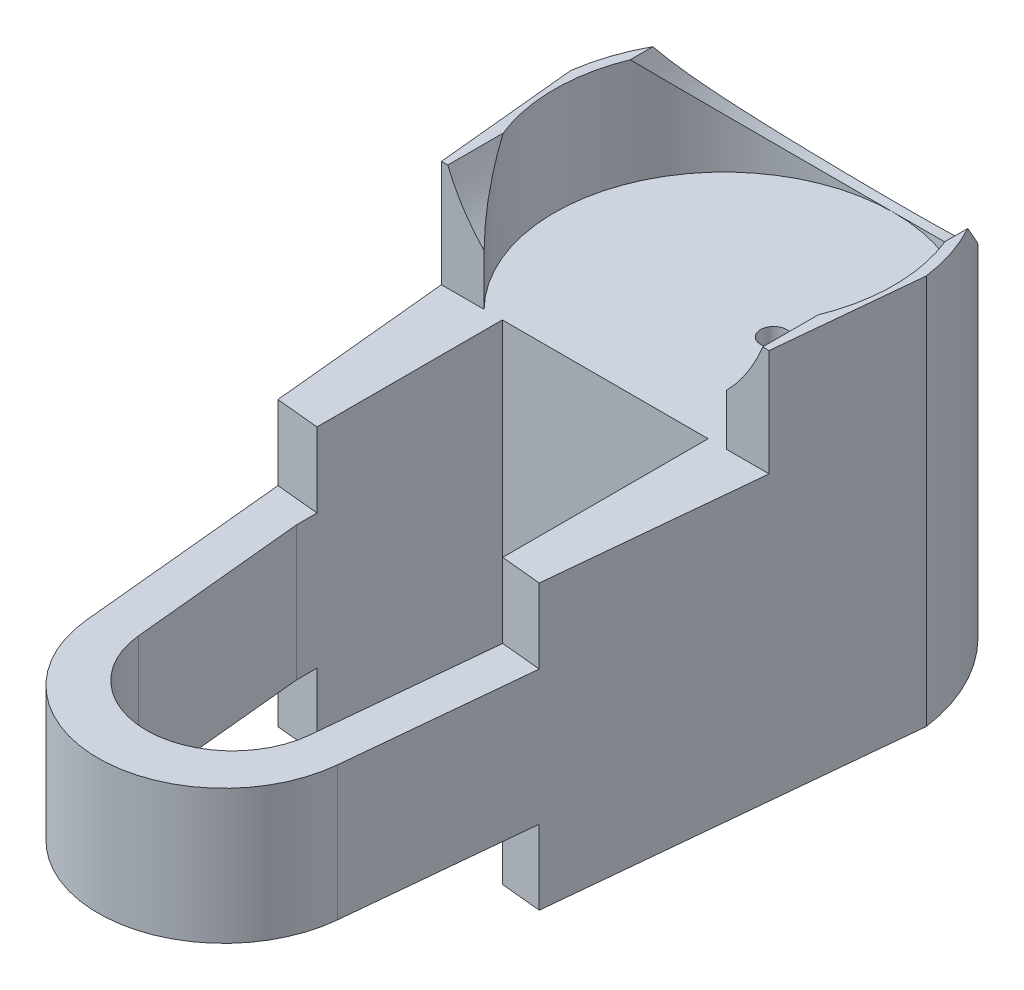
SolidWorks part; units mm, degrees
ref_plane "Front Plane" through (0, 0, 0) normal (0, 0, 1) x (1, 0, 0)
ref_plane "Top Plane" through (0, 0, 0) normal (0, 1, 0) x (1, 0, 0)
ref_plane "Right Plane" through (0, 0, 0) normal (1, 0, 0) x (0, 0, -1)
sketch "Sketch1" plane through (0, 0, 0) normal (0, 1, 0) x (1, 0, 0)
  line L0 (-21.209, -21.2151) -> (21.209, -21.2151)
  line L1 (-21.209, -21.209) -> (21.209, -21.209)
  line L2 (-21.209, -21.209) -> (-21.209, 21.209)
  line L3 (-21.209, 21.209) -> (21.209, 21.209)
  line L4 (21.209, -21.209) -> (21.209, 21.209)
  line L5 (-21.209, -21.209) -> (21.209, 21.209) construction
  line L6 (-21.209, 21.209) -> (21.209, -21.209) construction
  line L7 (-21.209, -21.2151) -> (-21.209, 21.2029)
  line L8 (-21.209, 21.2029) -> (21.209, 21.2029)
  line L9 (21.209, -21.2151) -> (21.209, 21.2029)
  line L10 (-21.209, -21.2151) -> (-4.8245, -4.8306) construction
  line L11 (-21.209, -66.9351) -> (21.209, -66.9351)
  line L12 (-36.6585, 5.0151) -> (-25.8562, -105.5982)
  line L13 (0, -55) -> (0, 55) construction
  line L14 (36.6585, 5.0151) -> (25.8562, -105.5982)
  line L15 (0.4439, 0.4378) -> (21.209, 21.2029) construction
  line L16 (-21.209, -66.929) -> (21.209, -66.929)
  line L17 (0.2749, -0.2809) -> (4.4443, -4.4503) construction
  line L18 (-21.209, -66.929) -> (-21.209, -24.511)
  line L19 (-21.209, -24.511) -> (21.209, -24.511)
  line L20 (21.209, -66.929) -> (21.209, -24.511)
  line L21 (-21.209, -66.9351) -> (-21.209, -24.5171)
  line L22 (-21.209, -24.5171) -> (21.209, -24.5171)
  line L23 (21.209, -66.9351) -> (21.209, -24.5171)
  line L24 (-21.209, -66.929) -> (21.209, -24.511) construction
  line L25 (-21.209, -24.511) -> (21.209, -66.929) construction
  line L26 (-21.209, -66.9351) -> (-4.8245, -50.5506) construction
  line L27 (0.4439, -45.2822) -> (21.209, -24.5171) construction
  arc A1 (-25.8562, -105.5982) -> (25.8562, -105.5982) centre (0, -103.0732) ccw
  arc A3 (36.6585, 5.0151) -> (-36.6585, 5.0151) centre (0, 0) ccw
  point P0 (0, 0)
  point P8 (0, -0.0061)
  point P17 (0, -45.72)
  point P30 (0, -45.7261)
  dimension "D5" = 37
  dimension "D1" = 42.418
  dimension "D2" = 42.418
  dimension "D3" = 2
  dimension "D4" = 2
extrude "Boss-Extrude1" add sketch "Sketch1" along normal blind 58.42 contours L14 A3 L12 A1 L4 L1 L2 L3 L9 L0 L7 L8 | L8 L2 L1 L4
sketch "Sketch2" plane through (0, 58.42, 0) normal (0, 1, 0) x (1, 0, 0)
  line L0 (-21.209, -66.9351) -> (-17.6812, -103.0584)
  line L3 (21.209, -66.9351) -> (17.6812, -103.0584)
  line L4 (-36.6585, 5.0151) -> (-25.8562, -105.5982) construction
  line L5 (36.6585, 5.0151) -> (25.8562, -105.5982) construction
  line L7 (-21.209, -66.9351) -> (21.209, -66.9351) construction
  line L8 (-21.209, -66.9351) -> (21.209, -66.9351)
  arc A0 (-17.6812, -103.0584) -> (17.6812, -103.0584) centre (0, -101.3316) ccw
  dimension "D1" = 180
  dimension "D2" = 180
sketch "Sketch3" plane through (35.8271, 0, 3.4988) normal (0.9953, 0, 0.0972) x (0.0972, 0, -0.9953)
  line L0 (-102.5851, 58.42) -> (-102.5851, 0) construction
  line L1 (-140.6851, 15.367) -> (-64.4851, 15.367)
  line L3 (-140.6851, 43.053) -> (-64.4851, 43.053)
  line L5 (-140.6851, 15.367) -> (-102.5851, 29.21) construction
  line L6 (-102.5851, 29.21) -> (-64.4851, 15.367) construction
  line L7 (-64.4851, 43.053) -> (-64.4851, 58.42)
  line L8 (8.5544, 58.42) -> (-102.5851, 58.42) construction
  line L9 (-64.4851, 58.42) -> (-140.6851, 58.42)
  line L10 (-140.6851, 58.42) -> (-140.6851, 43.053)
  line L11 (-140.6851, 0) -> (-64.4851, 0)
  line L12 (8.5544, 0) -> (-102.5851, 0) construction
  line L13 (-64.4851, 0) -> (-64.4851, 15.367)
  line L14 (-140.6851, 15.367) -> (-140.6851, 0)
  point P0 (-102.5851, 29.21)
  line M3 (-102.5851, 0) -> (8.5544, 0)
  line M6 (-102.5851, 58.42) -> (-102.5851, 0)
  dimension "D1" = 27.686
  dimension "D2" = 76.2
extrude "Cut-Extrude3" cut sketch "Sketch2" against normal blind 68.58 contours L0 A0 L3 L8
extrude "Cut-Extrude4" cut sketch "Sketch3" against normal through all contours L1 L14 L11 M6 | L13 L1 M3 M6 | L9 L10 L3 L7
ref_plane "Plane2" through (0, 0, 21.209) normal (0, 0, 1) x (1, 0, 0)
sketch "Sketch7" plane through (0, 0, 21.209) normal (0, 0, 1) x (1, 0, 0)
  line L0 (0, 58.42) -> (0, 93.35) construction
  line L1 (-21.209, 58.42) -> (21.209, 58.42) construction
  line L2 (-34.93, 59.9091) -> (-34.93, 93.35)
  line L3 (34.93, 59.9091) -> (34.93, 93.35)
  line L4 (-34.93, 59.9091) -> (34.93, 59.9091)
  line L5 (-34.93, 93.35) -> (34.93, 93.35)
  line L6 (-34.93, 59.9091) -> (-34.93, 55.4014)
  line L7 (-34.93, 55.4014) -> (34.93, 55.4014)
  line L8 (34.93, 55.4014) -> (34.93, 59.9091)
  line L9 (-34.93, 55.4014) -> (-40.0147, 55.4014)
  line L10 (-40.0147, 55.4014) -> (-40.0147, 94.2075)
  line L11 (-34.93, 93.35) -> (-40.0147, 94.2075)
  line L12 (34.93, 55.4014) -> (41.4804, 55.4014)
  line L13 (41.4804, 55.4014) -> (41.4804, 93.35)
  line L14 (41.4804, 93.35) -> (34.93, 93.35)
  arc A0 (-34.93, 93.35) -> (34.93, 93.35) centre (0, 93.35) ccw
  dimension "D1" = 34.93
extrude "Boss-Extrude6" add sketch "Sketch7" against normal blind 60 and the other way up to surface (3.302 mm away) contours A0 L2 L4 | L7 L8 L4 L6 | A0 L4 L3 | L2 L11 L10 L9 L6 | L13 L14 L3 L8 L12
sketch "Sketch9" plane through (0, 0, 0) normal (0, -1, 0) x (1, 0, 0)
  line L0 (36.6585, -5.0151) -> (29.5593, 67.6786) construction
  line L1 (-36.6585, -5.0151) -> (-30.1286, 61.8496) construction
  line L2 (36.6585, -5.0151) -> (29.5593, 67.6786)
  line L3 (-36.6585, -5.0151) -> (-30.1286, 61.8496)
  line L4 (29.5593, 67.6786) -> (73.6606, -15.3241)
  line L5 (73.6606, -15.3241) -> (14.2721, -84.2116)
  line L6 (14.2721, -84.2116) -> (-60.0286, -39.8694)
  line L7 (-60.0286, -39.8694) -> (-30.1286, 61.8496)
  arc A0 (-36.6585, -5.0151) -> (36.6585, -5.0151) centre (0, 0) ccw construction
  arc A1 (-36.6585, -5.0151) -> (36.6585, -5.0151) centre (0, 0) ccw
extrude "Cut-Extrude9" cut sketch "Sketch9" against normal blind 106
sketch "Sketch4" plane through (0, 58.42, 0) normal (0, 1, 0) x (1, 0, 0)
  line L0 (9.8, -24.511) -> (9.8, 0.389) construction
  circle A0 centre (9.8, 0.389) radius 2.667
  dimension "D2" = 5.334
  dimension "D1" = 24.9
extrude "Cut-Extrude6" cut sketch "Sketch4" against normal blind 20 and the other way blind 106
sketch "Sketch10" plane through (35.8271, 0, 3.4988) normal (0.9953, 0, 0.0972) x (0.0972, 0, -0.9953)
  line L0 (-21.1121, 80.4421) -> (1.8262, 80.4421)
  line L1 (-21.1121, 58.42) -> (-21.1121, 84.4421) construction
  line L2 (-21.1121, 80.4421) -> (-21.1121, 84.4421)
  line L3 (1.8262, 80.4421) -> (48.3524, 80.4421)
  line L4 (48.3524, 80.4421) -> (47.2155, 104.0447)
  line L5 (47.2155, 104.0447) -> (-21.1121, 100.7536)
  line L6 (-21.1121, 100.7536) -> (-21.1121, 84.4421)
  line L7 (-21.1121, 80.4421) -> (-34.4127, 80.4421)
  line L8 (-34.4127, 80.4421) -> (-34.4127, 100.7536)
  line L9 (-34.4127, 100.7536) -> (-21.1121, 100.7536)
  line M10 (8.5544, 0) -> (8.5544, 93.35)
  ellipse M11 centre (-368.6038, 93.35) end of major axis (-9.2296, 93.35) minor radius 34.93 (-9.2296, 93.35) -> (-21.1121, 84.4421) cw
  line M12 (-21.1121, 84.4421) -> (-21.1121, 58.42)
  dimension "D1" = 4
extrude "Cut-Extrude13" cut sketch "Sketch10" against normal blind 106 contours L0 L3 M10 M11 M12 | L5 L6 L3 L4 M11 M10 | L9 L8 L7 L6 M12
sketch "Sketch11" plane through (0, 58.42, 0) normal (0, 1, 0) x (1, 0, 0)
  circle A1 centre (0, 0) radius 35
  dimension "D1" = 70
extrude "Cut-Extrude15" cut sketch "Sketch11" along normal blind 106
